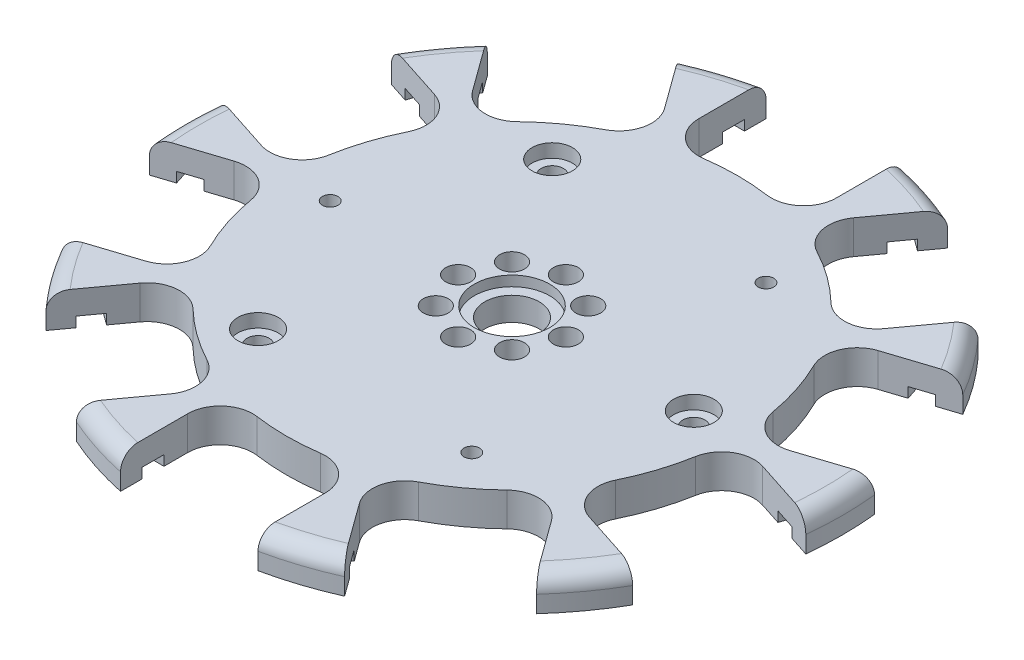
SolidWorks part; units mm, degrees
material "Delrin 2700 NC010, Low Viscosity Acetal Copolymer (SS)"
ref_plane "Front Plane" through (0, 0, 0) normal (0, 0, 1) x (1, 0, 0)
ref_plane "Top Plane" through (0, 0, 0) normal (0, 1, 0) x (1, 0, 0)
ref_plane "Right Plane" through (0, 0, 0) normal (1, 0, 0) x (0, 0, -1)
ref_plane "Plane1" through (0, 0, 0) normal (0, 0, -1) x (-1, 0, 0)
sketch "Sketch1" plane through (0, 0, 0) normal (0, 0, -1) x (-1, 0, 0)
  line L0 (-49, 0) -> (0, 0)
  line L1 (0, 0) -> (0, 5)
  line L2 (0, 5) -> (-49, 5)
  line L3 (-49, 5) -> (-49, 0)
  line L4 (0, 0) -> (0, 5) construction
revolve "Revolve1" add sketch "Sketch1" angle 360 about L4
sketch "Sketch2" plane through (0, 0, 0) normal (0, -1, 0) x (1, 0, 0)
  line L0 (-10.205, 47.9255) -> (-10.205, 31.9078)
  line L1 (10.205, 31.9078) -> (10.205, 47.9255)
  arc A0 (10.205, 47.9255) -> (-10.205, 47.9255) centre (0, 0) ccw
  arc A1 (-10.205, 31.9078) -> (10.205, 31.9078) centre (0, 0) cw
extrude "Cut-Extrude1" cut sketch "Sketch2" against normal through all
sketch "Sketch3" plane through (0, 0, 0) normal (0, -1, 0) x (1, 0, 0)
  line L0 (19.9139, 44.7709) -> (10.4989, 31.8123)
  line L1 (27.011, 19.8156) -> (36.4259, 32.7742)
  arc A0 (36.4259, 32.7742) -> (19.9139, 44.7709) centre (0, 0) ccw
  arc A1 (10.4989, 31.8123) -> (27.011, 19.8156) centre (0, 0) cw
extrude "Cut-Extrude2" cut sketch "Sketch3" against normal through all
sketch "Sketch4" plane through (0, 0, 0) normal (0, -1, 0) x (1, 0, 0)
  line L0 (42.4264, 24.5153) -> (27.1926, 19.5656)
  line L1 (33.4996, 0.1545) -> (48.7334, 5.1043)
  arc A0 (48.7334, 5.1043) -> (42.4264, 24.5153) centre (0, 0) ccw
  arc A1 (27.1926, 19.5656) -> (33.4996, 0.1545) centre (0, 0) cw
extrude "Cut-Extrude3" cut sketch "Sketch4" against normal through all
sketch "Sketch5" plane through (0, 0, 0) normal (0, -1, 0) x (1, 0, 0)
  line L0 (48.7334, -5.1043) -> (33.4996, -0.1545)
  line L1 (27.1926, -19.5656) -> (42.4264, -24.5153)
  arc A0 (42.4264, -24.5153) -> (48.7334, -5.1043) centre (0, 0) ccw
  arc A1 (33.4996, -0.1545) -> (27.1926, -19.5656) centre (0, 0) cw
extrude "Cut-Extrude4" cut sketch "Sketch5" against normal through all
sketch "Sketch6" plane through (0, 0, 0) normal (0, -1, 0) x (1, 0, 0)
  line L0 (36.4259, -32.7742) -> (27.011, -19.8156)
  line L1 (10.4989, -31.8123) -> (19.9139, -44.7709)
  arc A0 (19.9139, -44.7709) -> (36.4259, -32.7742) centre (0, 0) ccw
  arc A1 (27.011, -19.8156) -> (10.4989, -31.8123) centre (0, 0) cw
extrude "Cut-Extrude5" cut sketch "Sketch6" against normal through all
sketch "Sketch7" plane through (0, 0, 0) normal (0, -1, 0) x (1, 0, 0)
  line L0 (10.205, -47.9255) -> (10.205, -31.9078)
  line L1 (-10.205, -31.9078) -> (-10.205, -47.9255)
  arc A0 (-10.205, -47.9255) -> (10.205, -47.9255) centre (0, 0) ccw
  arc A1 (10.205, -31.9078) -> (-10.205, -31.9078) centre (0, 0) cw
extrude "Cut-Extrude6" cut sketch "Sketch7" against normal through all
sketch "Sketch8" plane through (0, 0, 0) normal (0, -1, 0) x (1, 0, 0)
  line L0 (-19.9139, -44.7709) -> (-10.4989, -31.8123)
  line L1 (-27.011, -19.8156) -> (-36.4259, -32.7742)
  arc A0 (-36.4259, -32.7742) -> (-19.9139, -44.7709) centre (0, 0) ccw
  arc A1 (-10.4989, -31.8123) -> (-27.011, -19.8156) centre (0, 0) cw
extrude "Cut-Extrude7" cut sketch "Sketch8" against normal through all
sketch "Sketch9" plane through (0, 0, 0) normal (0, -1, 0) x (1, 0, 0)
  line L0 (-42.4264, -24.5153) -> (-27.1926, -19.5656)
  line L1 (-33.4996, -0.1545) -> (-48.7334, -5.1043)
  arc A0 (-48.7334, -5.1043) -> (-42.4264, -24.5153) centre (0, 0) ccw
  arc A1 (-27.1926, -19.5656) -> (-33.4996, -0.1545) centre (0, 0) cw
extrude "Cut-Extrude8" cut sketch "Sketch9" against normal through all
sketch "Sketch10" plane through (0, 0, 0) normal (0, -1, 0) x (1, 0, 0)
  line L0 (-48.7334, 5.1043) -> (-33.4996, 0.1545)
  line L1 (-27.1926, 19.5656) -> (-42.4264, 24.5153)
  arc A0 (-42.4264, 24.5153) -> (-48.7334, 5.1043) centre (0, 0) ccw
  arc A1 (-33.4996, 0.1545) -> (-27.1926, 19.5656) centre (0, 0) cw
extrude "Cut-Extrude9" cut sketch "Sketch10" against normal through all
sketch "Sketch11" plane through (0, 0, 0) normal (0, -1, 0) x (1, 0, 0)
  line L0 (-36.4259, 32.7742) -> (-27.011, 19.8156)
  line L1 (-10.4989, 31.8123) -> (-19.9139, 44.7709)
  arc A0 (-19.9139, 44.7709) -> (-36.4259, 32.7742) centre (0, 0) ccw
  arc A1 (-27.011, 19.8156) -> (-10.4989, 31.8123) centre (0, 0) cw
extrude "Cut-Extrude10" cut sketch "Sketch11" against normal through all
sketch "Sketch12" plane through (8.256, 0, 5.9983) normal (-0.809, 0, -0.5878) x (-0.5878, 0, 0.809)
  line L0 (44.73, 0) -> (44.73, 1.5)
  line L1 (44.73, 1.5) -> (41.48, 1.5)
  line L2 (41.48, 1.5) -> (41.48, 0)
  line L3 (41.48, 0) -> (44.73, 0)
extrude "Cut-Extrude11" cut sketch "Sketch12" against normal blind 2.772
sketch "Sketch13" plane through (-10.205, 0, 0) normal (1, 0, 0) x (0, 0, -1)
  line L0 (-41.48, 0) -> (-41.48, 1.5)
  line L1 (-41.48, 1.5) -> (-44.73, 1.5)
  line L2 (-44.73, 1.5) -> (-44.73, 0)
  line L3 (-44.73, 0) -> (-41.48, 0)
extrude "Cut-Extrude12" cut sketch "Sketch13" against normal blind 2.772
sketch "Sketch14" plane through (10.205, 0, 0) normal (-1, 0, 0) x (0, 0, 1)
  line L0 (44.73, 0) -> (44.73, 1.5)
  line L1 (44.73, 1.5) -> (41.48, 1.5)
  line L2 (41.48, 1.5) -> (41.48, 0)
  line L3 (41.48, 0) -> (44.73, 0)
extrude "Cut-Extrude13" cut sketch "Sketch14" against normal blind 2.772
sketch "Sketch15" plane through (-8.256, 0, 5.9983) normal (0.809, 0, -0.5878) x (-0.5878, 0, -0.809)
  line L0 (-41.48, 0) -> (-41.48, 1.5)
  line L1 (-41.48, 1.5) -> (-44.73, 1.5)
  line L2 (-44.73, 1.5) -> (-44.73, 0)
  line L3 (-44.73, 0) -> (-41.48, 0)
extrude "Cut-Extrude14" cut sketch "Sketch15" against normal blind 2.772
sketch "Sketch16" plane through (8.256, 0, -5.9983) normal (-0.809, 0, 0.5878) x (0.5878, 0, 0.809)
  line L0 (44.73, 0) -> (44.73, 1.5)
  line L1 (44.73, 1.5) -> (41.48, 1.5)
  line L2 (41.48, 1.5) -> (41.48, 0)
  line L3 (41.48, 0) -> (44.73, 0)
extrude "Cut-Extrude15" cut sketch "Sketch16" against normal blind 2.772
sketch "Sketch17" plane through (-3.1535, 0, 9.7055) normal (0.309, 0, -0.9511) x (-0.9511, 0, -0.309)
  line L0 (-41.48, 0) -> (-41.48, 1.5)
  line L1 (-41.48, 1.5) -> (-44.73, 1.5)
  line L2 (-44.73, 1.5) -> (-44.73, 0)
  line L3 (-44.73, 0) -> (-41.48, 0)
extrude "Cut-Extrude16" cut sketch "Sketch17" against normal blind 2.772
sketch "Sketch18" plane through (3.1535, 0, -9.7055) normal (-0.309, 0, 0.9511) x (0.9511, 0, 0.309)
  line L0 (44.73, 0) -> (44.73, 1.5)
  line L1 (44.73, 1.5) -> (41.48, 1.5)
  line L2 (41.48, 1.5) -> (41.48, 0)
  line L3 (41.48, 0) -> (44.73, 0)
extrude "Cut-Extrude17" cut sketch "Sketch18" against normal blind 2.772
sketch "Sketch19" plane through (3.1535, 0, 9.7055) normal (-0.309, 0, -0.9511) x (-0.9511, 0, 0.309)
  line L0 (-41.48, 0) -> (-41.48, 1.5)
  line L1 (-41.48, 1.5) -> (-44.73, 1.5)
  line L2 (-44.73, 1.5) -> (-44.73, 0)
  line L3 (-44.73, 0) -> (-41.48, 0)
extrude "Cut-Extrude18" cut sketch "Sketch19" against normal blind 2.772
sketch "Sketch20" plane through (-3.1535, 0, -9.7055) normal (0.309, 0, 0.9511) x (0.9511, 0, -0.309)
  line L0 (44.73, 0) -> (44.73, 1.5)
  line L1 (44.73, 1.5) -> (41.48, 1.5)
  line L2 (41.48, 1.5) -> (41.48, 0)
  line L3 (41.48, 0) -> (44.73, 0)
extrude "Cut-Extrude19" cut sketch "Sketch20" against normal blind 2.772
sketch "Sketch21" plane through (8.256, 0, 5.9983) normal (-0.809, 0, -0.5878) x (-0.5878, 0, 0.809)
  line L0 (-41.48, 0) -> (-41.48, 1.5)
  line L1 (-41.48, 1.5) -> (-44.73, 1.5)
  line L2 (-44.73, 1.5) -> (-44.73, 0)
  line L3 (-44.73, 0) -> (-41.48, 0)
extrude "Cut-Extrude20" cut sketch "Sketch21" against normal blind 2.772
sketch "Sketch22" plane through (-8.256, 0, -5.9983) normal (0.809, 0, 0.5878) x (0.5878, 0, -0.809)
  line L0 (44.73, 0) -> (44.73, 1.5)
  line L1 (44.73, 1.5) -> (41.48, 1.5)
  line L2 (41.48, 1.5) -> (41.48, 0)
  line L3 (41.48, 0) -> (44.73, 0)
extrude "Cut-Extrude21" cut sketch "Sketch22" against normal blind 2.772
sketch "Sketch23" plane through (10.205, 0, 0) normal (-1, 0, 0) x (0, 0, 1)
  line L0 (-41.48, 0) -> (-41.48, 1.5)
  line L1 (-41.48, 1.5) -> (-44.73, 1.5)
  line L2 (-44.73, 1.5) -> (-44.73, 0)
  line L3 (-44.73, 0) -> (-41.48, 0)
extrude "Cut-Extrude22" cut sketch "Sketch23" against normal blind 2.772
sketch "Sketch24" plane through (-10.205, 0, 0) normal (1, 0, 0) x (0, 0, -1)
  line L0 (44.73, 0) -> (44.73, 1.5)
  line L1 (44.73, 1.5) -> (41.48, 1.5)
  line L2 (41.48, 1.5) -> (41.48, 0)
  line L3 (41.48, 0) -> (44.73, 0)
extrude "Cut-Extrude23" cut sketch "Sketch24" against normal blind 2.772
sketch "Sketch25" plane through (8.256, 0, -5.9983) normal (-0.809, 0, 0.5878) x (0.5878, 0, 0.809)
  line L0 (-41.48, 0) -> (-41.48, 1.5)
  line L1 (-41.48, 1.5) -> (-44.73, 1.5)
  line L2 (-44.73, 1.5) -> (-44.73, 0)
  line L3 (-44.73, 0) -> (-41.48, 0)
extrude "Cut-Extrude24" cut sketch "Sketch25" against normal blind 2.772
sketch "Sketch26" plane through (-8.256, 0, 5.9983) normal (0.809, 0, -0.5878) x (-0.5878, 0, -0.809)
  line L0 (44.73, 0) -> (44.73, 1.5)
  line L1 (44.73, 1.5) -> (41.48, 1.5)
  line L2 (41.48, 1.5) -> (41.48, 0)
  line L3 (41.48, 0) -> (44.73, 0)
extrude "Cut-Extrude25" cut sketch "Sketch26" against normal blind 2.772
sketch "Sketch27" plane through (3.1535, 0, -9.7055) normal (-0.309, 0, 0.9511) x (0.9511, 0, 0.309)
  line L0 (-41.48, 0) -> (-41.48, 1.5)
  line L1 (-41.48, 1.5) -> (-44.73, 1.5)
  line L2 (-44.73, 1.5) -> (-44.73, 0)
  line L3 (-44.73, 0) -> (-41.48, 0)
extrude "Cut-Extrude26" cut sketch "Sketch27" against normal blind 2.772
sketch "Sketch28" plane through (-3.1535, 0, 9.7055) normal (0.309, 0, -0.9511) x (-0.9511, 0, -0.309)
  line L0 (44.73, 0) -> (44.73, 1.5)
  line L1 (44.73, 1.5) -> (41.48, 1.5)
  line L2 (41.48, 1.5) -> (41.48, 0)
  line L3 (41.48, 0) -> (44.73, 0)
extrude "Cut-Extrude27" cut sketch "Sketch28" against normal blind 2.772
sketch "Sketch29" plane through (-3.1535, 0, -9.7055) normal (0.309, 0, 0.9511) x (0.9511, 0, -0.309)
  line L0 (-41.48, 0) -> (-41.48, 1.5)
  line L1 (-41.48, 1.5) -> (-44.73, 1.5)
  line L2 (-44.73, 1.5) -> (-44.73, 0)
  line L3 (-44.73, 0) -> (-41.48, 0)
extrude "Cut-Extrude28" cut sketch "Sketch29" against normal blind 2.772
sketch "Sketch30" plane through (3.1535, 0, 9.7055) normal (-0.309, 0, -0.9511) x (-0.9511, 0, 0.309)
  line L0 (44.73, 0) -> (44.73, 1.5)
  line L1 (44.73, 1.5) -> (41.48, 1.5)
  line L2 (41.48, 1.5) -> (41.48, 0)
  line L3 (41.48, 0) -> (44.73, 0)
extrude "Cut-Extrude29" cut sketch "Sketch30" against normal blind 2.772
sketch "Sketch31" plane through (-8.256, 0, -5.9983) normal (0.809, 0, 0.5878) x (0.5878, 0, -0.809)
  line L0 (-41.48, 0) -> (-41.48, 1.5)
  line L1 (-41.48, 1.5) -> (-44.73, 1.5)
  line L2 (-44.73, 1.5) -> (-44.73, 0)
  line L3 (-44.73, 0) -> (-41.48, 0)
extrude "Cut-Extrude30" cut sketch "Sketch31" against normal blind 2.772
hole_wizard "Ø2.3 (2.3) Diameter Hole1" positions "Sketch33" profile "Sketch32" hole size "Ø2.3" standard "ANSI Metric"
sketch "Sketch33" plane through (0, 0, 0) normal (0, -1, 0) x (-1, 0, 0)
  point P0 (27, 0)
  point P1 (-15.8702, 21.8435)
  point P2 (-15.8702, -21.8435)
sketch "Sketch32" plane through (-27, 0, 0) normal (1, 0, 0) x (0, 0, -1)
  line L0 (0, 0) -> (0, 5)
  line L1 (0, 5) -> (1.15, 5)
  line L2 (1.15, 5) -> (1.15, 0)
  line L5 (1.15, 0) -> (0, 0)
  line L11 (0, -6.35) -> (0, 107.95) construction
  dimension "Thru Hole Dia." = 2.3
  dimension "Thru Hole Depth" = 5
hole_wizard "Ø3.7 (3.7) Diameter Hole1" positions "Sketch35" profile "Sketch34" hole size "Ø3.7" standard "ANSI Metric"
sketch "Sketch35" plane through (0, 0, 0) normal (0, -1, 0) x (-1, 0, 0)
  point P0 (8, 0)
  point P1 (5.6569, -5.6569)
  point P2 (0, -8)
  point P3 (-5.6569, -5.6569)
  point P4 (-8, 0)
  point P5 (-5.6569, 5.6569)
  point P6 (0, 8)
  point P7 (5.6569, 5.6569)
sketch "Sketch34" plane through (-8, 0, 0) normal (1, 0, 0) x (0, 0, -1)
  line L0 (0, 0) -> (0, 5)
  line L1 (0, 5) -> (1.85, 5)
  line L2 (1.85, 5) -> (1.85, 0)
  line L5 (1.85, 0) -> (0, 0)
  line L11 (0, -6.35) -> (0, 107.95) construction
  dimension "Thru Hole Dia." = 3.7
  dimension "Thru Hole Depth" = 5
hole_wizard "CBORE for M3 Hex Head Machine Screw1" positions "Sketch37" profile "Sketch36" counterbore size "M3" standard "ANSI Metric"
sketch "Sketch37" plane through (0, 5, 0) normal (0, 1, 0) x (1, 0, 0)
  point P0 (-15.8702, 21.8435)
  point P1 (-15.8702, -21.8435)
  point P2 (27, 0)
sketch "Sketch36" plane through (-15.8702, 5, -21.8435) normal (1, 0, 0) x (0, 0, 1)
  line L0 (0, 0) -> (0, 5)
  line L1 (0, 5) -> (1.65, 5)
  line L3 (1.65, 5) -> (1.65, 2)
  line L4 (1.65, 2) -> (3, 2)
  line L5 (3, 2) -> (3, 0)
  line L7 (3, 0) -> (0, 0)
  line L11 (0, -6.35) -> (0, 107.95) construction
  dimension "Thru Hole Dia." = 3.3
  dimension "Thru Hole Depth" = 5
  dimension "C'Bore Dia." = 6
  dimension "C'Bore Depth" = 2
hole_wizard "Hole1" positions "Sketch39" profile "Sketch38" legacy
sketch "Sketch39" plane through (0, 5, 0) normal (0, 1, 0) x (1, 0, 0)
  point P0 (0, 0)
sketch "Sketch38" plane through (0, 5, 0) normal (1, 0, 0) x (0, 0, 1)
  line L0 (0, 0) -> (0, 5)
  line L1 (0, 5) -> (4.05, 5)
  line L2 (4.05, 5) -> (4.05, 1.5)
  line L3 (4.05, 1.5) -> (5.6, 1.5)
  line L4 (5.6, 1.5) -> (5.6, 0)
  line L5 (5.6, 0) -> (0, 0)
  line L6 (0, 110) -> (0, -10) construction
  dimension "Diameter" = 8.1
  dimension "Depth" = 5
  dimension "C-Bore Diameter" = 11.2
  dimension "C-Bore Depth" = 1.5
fillet "Fillet1" radius 2.5 10 edges at (-39.6418, 5, -28.8015) (15.1418, 5, -46.6018) (-39.6418, 5, 28.8015) (39.6418, 5, 28.8015) (-15.1418, 5, -46.6018) (49, 5, 0) (-49, 5, 0) (39.6418, 5, -28.8015) (15.1418, 5, 46.6018) (-15.1418, 5, 46.6018)
fillet "Fillet2" radius 4.827 20 edges at (-27.011, 2.5, -19.8156) (10.4989, 2.5, -31.8123) (-27.1926, 2.5, 19.5656) (-27.011, 2.5, 19.8156) (-10.205, 2.5, -31.9078) (-10.4989, 2.5, 31.8123) (-33.4996, 2.5, -0.1545) (-10.205, 2.5, 31.9078) (27.011, 2.5, -19.8156) (10.205, 2.5, 31.9078) (10.205, 2.5, -31.9078) (27.011, 2.5, 19.8156) (-10.4989, 2.5, -31.8123) (27.1926, 2.5, 19.5656) (-27.1926, 2.5, -19.5656) (33.4996, 2.5, 0.1545) (-33.4996, 2.5, 0.1545) (33.4996, 2.5, -0.1545) (27.1926, 2.5, -19.5656) (10.4989, 2.5, 31.8123)
